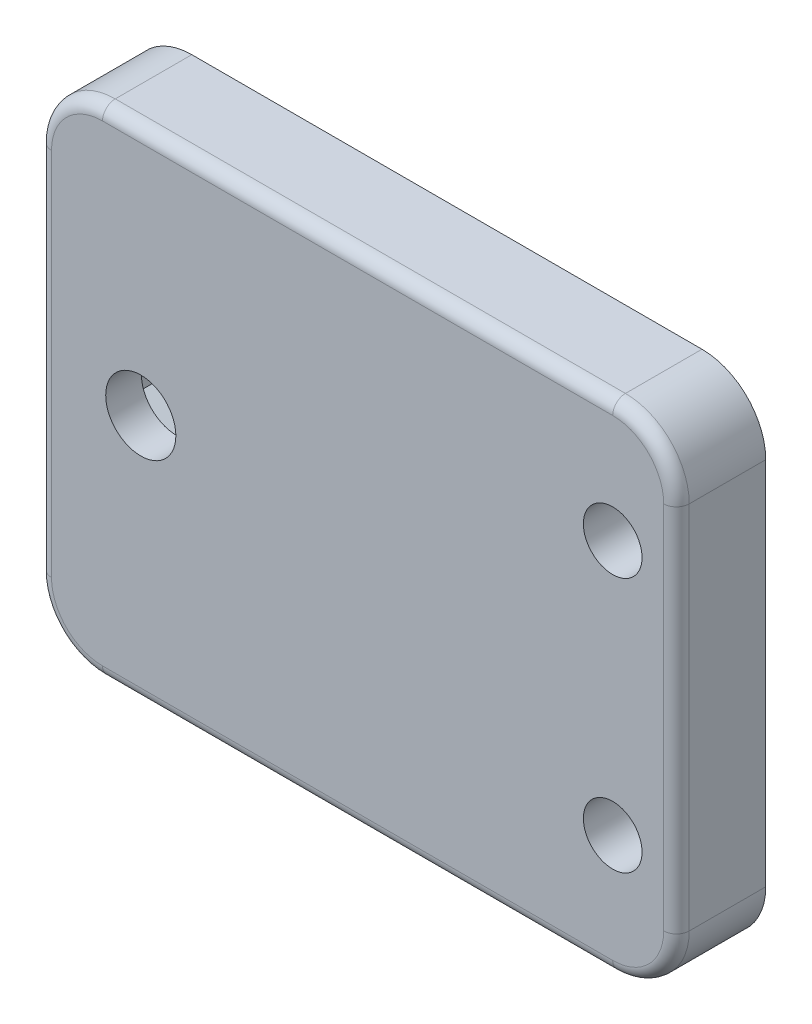
SolidWorks part; units mm, degrees
ref_plane "Front Plane" through (0, 0, 0) normal (0, 0, 1) x (1, 0, 0)
ref_plane "Top Plane" through (0, 0, 0) normal (0, 1, 0) x (1, 0, 0)
ref_plane "Right Plane" through (0, 0, 0) normal (1, 0, 0) x (0, 0, -1)
sketch "Sketch1" plane through (0, 0, 0) normal (0, 0, 1) x (1, 0, 0)
  line L0 (-17, 0) -> (0, 0) construction
  line L1 (-25, -19.5) -> (25, -19.5)
  line L2 (-25, -19.5) -> (-25, 19.5)
  line L3 (-25, 19.5) -> (25, 19.5)
  line L4 (25, -19.5) -> (25, 19.5)
  line L5 (-25, -19.5) -> (25, 19.5) construction
  line L6 (-25, 19.5) -> (25, -19.5) construction
  line L7 (20, 10) -> (20, -10) construction
  line L8 (0, 0) -> (20, 0) construction
  circle A0 centre (-17, 0) radius 2.75
  circle A1 centre (20, 10) radius 2.3
  circle A2 centre (20, -10) radius 2.3
  point P0 (0, 0)
  dimension "D1" = 5.5
  dimension "D6" = 4.6
  dimension "D2" = 42
  dimension "D3" = 8
  dimension "D4" = 39
  dimension "D5" = 20
  dimension "D7" = 5
extrude "Boss-Extrude1" add sketch "Sketch1" along normal blind 7
sketch "Sketch2" plane through (0, 0, 0) normal (0, 0, -1) x (-1, 0, 0)
  line L1 (17, 4.6765) -> (12.95, 2.3383)
  line L2 (12.95, 2.3383) -> (12.95, -2.3383)
  line L3 (12.95, -2.3383) -> (17, -4.6765)
  line L4 (17, -4.6765) -> (21.05, -2.3383)
  line L5 (21.05, -2.3383) -> (21.05, 2.3383)
  line L6 (21.05, 2.3383) -> (17, 4.6765)
  circle A0 centre (17, 0) radius 4.05 construction
  dimension "D1" = 8.1
extrude "Cut-Extrude1" cut sketch "Sketch2" against normal blind 4.2
fillet "Fillet1" radius 5 4 edges at (25, -19.5, 3.5) (-25, -19.5, 3.5) (-25, 19.5, 3.5) (25, 19.5, 3.5)
sketch "Sketch3" plane through (0, 0, 0) normal (0, 0, -1) x (-1, 0, 0)
  line L0 (-20, 10) -> (-12.5, 10) construction
  line L1 (-16.5, 7.5) -> (-8.5, 7.5)
  line L2 (-16.5, 7.5) -> (-16.5, 12.5)
  line L3 (-16.5, 12.5) -> (-8.5, 12.5)
  line L4 (-8.5, 7.5) -> (-8.5, 12.5)
  line L5 (-16.5, 7.5) -> (-8.5, 12.5) construction
  line L6 (-16.5, 12.5) -> (-8.5, 7.5) construction
  point P0 (-12.5, 10)
  dimension "D1" = 5
  dimension "D2" = 3.5
  dimension "D3" = 8
extrude "Boss-Extrude2" add sketch "Sketch3" along normal blind 4
mirror "Mirror1" about plane through (0, 0, 0) normal (0, 1, 0) of "Boss-Extrude2"
fillet "Fillet2" radius 1 4 edges at (16.5, 7.5, -2) (8.5, 7.5, -2) (8.5, 12.5, -2) (16.5, 12.5, -2)
fillet "Fillet3" radius 1 4 edges at (16.5, -12.5, -2) (8.5, -12.5, -2) (8.5, -7.5, -2) (16.5, -7.5, -2)
fillet "Fillet4" radius 1 8 edges at (-23.5355, 18.0355, 7) (0, 19.5, 7) (23.5355, 18.0355, 7) (25, 0, 7) (23.5355, -18.0355, 7) (0, -19.5, 7) (-23.5355, -18.0355, 7) (-25, 0, 7)
